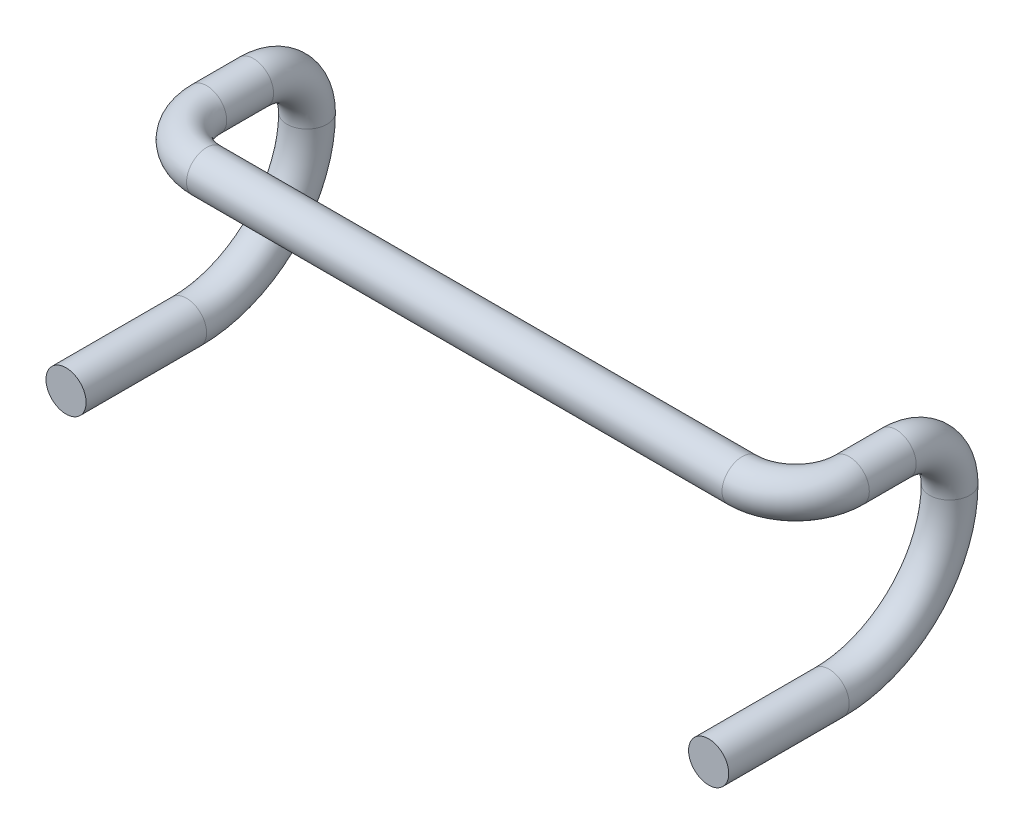
SolidWorks part; units mm, degrees
ref_plane "Front Plane" through (0, 0, 0) normal (0, 0, 1) x (1, 0, 0)
ref_plane "Top Plane" through (0, 0, 0) normal (0, 1, 0) x (1, 0, 0)
ref_plane "Right Plane" through (0, 0, 0) normal (1, 0, 0) x (0, 0, -1)
sketch "Sketch1" plane through (0, 0, 0) normal (0, 1, 0) x (1, 0, 0)
  line L0 (0, 0) -> (-200, 0)
  line L1 (-200, 0) -> (-200, 40) construction
  line L2 (-200, 40) -> (-240, 40) construction
  arc A0 (-200, 0) -> (-240, 40) centre (-200, 40) cw
  dimension "D1" = 200
  dimension "D2" = 40
ref_plane "Plane1" through (-240, 0, 0) normal (1, 0, 0) x (0, 0, -1)
sketch "Sketch2" plane through (-240, 0, 0) normal (1, 0, 0) x (0, 0, -1)
  line L0 (40, 0) -> (75, 0)
  line L1 (75, 0) -> (75, -40) construction
  line L2 (115, -40) -> (25, -40) construction
  line L3 (25, -40) -> (25, -130) construction
  arc A0 (75, 0) -> (115, -40) centre (75, -40) cw
  arc A1 (115, -40) -> (25, -130) centre (25, -40) cw
  dimension "D1" = 35
  dimension "D2" = 40
  dimension "D3" = 90
sketch "Sketch3" plane through (-240, 0, 0) normal (1, 0, 0) x (0, 0, -1)
  line L0 (25, -130) -> (-65, -130)
  dimension "D1" = 90
ref_plane "Plane2" through (0, 0, 65) normal (0, 0, 1) x (1, 0, 0)
sweep "Sweep4" add path "Sketch1" circular profile diameter 30 parameters "D3"=30
sweep "Sweep5" add path "Sketch2" circular profile diameter 30 parameters "D3"=30
sweep "Sweep6" add path "Sketch3" circular profile diameter 30 parameters "D3"=30
mirror "Mirror1" about plane through (0, 0, 0) normal (1, 0, 0) of "Sweep6", "Sweep5", "Sweep4"
